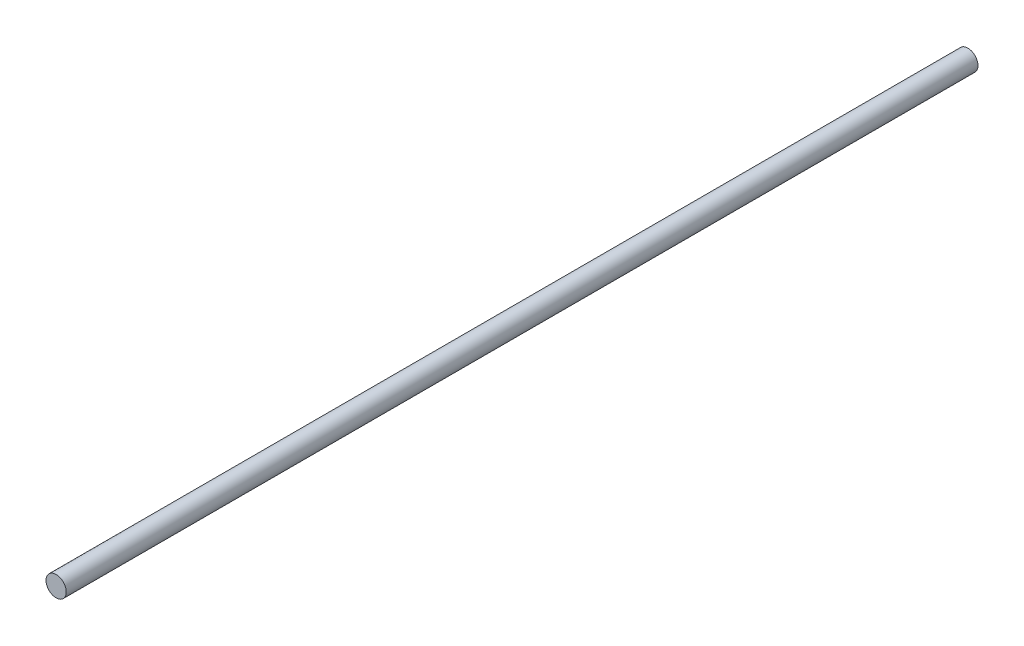
SolidWorks part; units mm, degrees
ref_plane "Plan de face" through (0, 0, 0) normal (0, 0, 1) x (1, 0, 0)
ref_plane "Plan de dessus" through (0, 0, 0) normal (0, 1, 0) x (1, 0, 0)
ref_plane "Plan de droite" through (0, 0, 0) normal (1, 0, 0) x (0, 0, -1)
sketch "Esquisse1" plane through (0, 0, 0) normal (0, 0, 1) x (1, 0, 0)
  circle A0 centre (0, 0) radius 4
  dimension "D1" = 8
sketch "Esquisse2" plane through (0, 0, 0) normal (0, 1, 0) x (1, 0, 0)
  line L0 (0, 0) -> (0, 360)
  line L3 (4, 360) -> (-4, 360) construction
  point P4 (0, 360)
sweep "Balayage1" add profiles "Esquisse1" path "Esquisse2"
